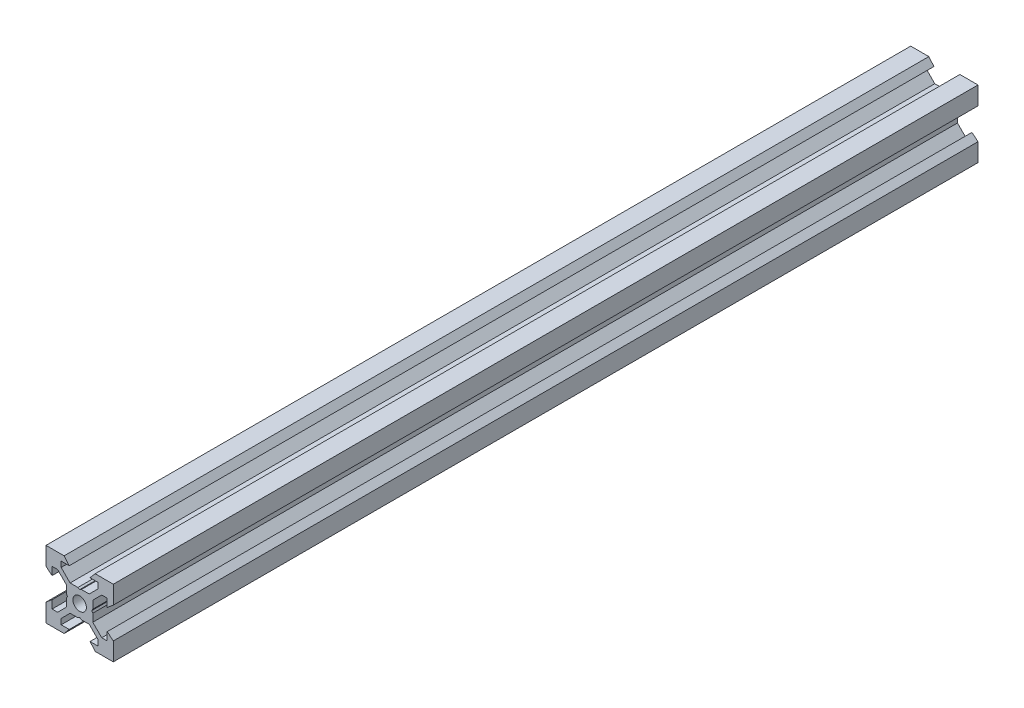
SolidWorks part; units mm, degrees
ref_plane "Front Plane" through (0, 0, 0) normal (0, 0, 1) x (1, 0, 0)
ref_plane "Top Plane" through (0, 0, 0) normal (0, 1, 0) x (1, 0, 0)
ref_plane "Right Plane" through (0, 0, 0) normal (1, 0, 0) x (0, 0, -1)
sketch "Sketch1" plane through (0, 0, 0) normal (0, 0, 1) x (1, 0, 0)
  line L0 (10, 10) -> (4.6104, 10) construction
  line L1 (10, 10) -> (10, 4.6104) construction
  line L2 (10, -10) -> (10, -4.6104) construction
  line L3 (10, -10) -> (4.6104, -10) construction
  line L4 (10, 10) -> (10, 4.6104)
  line L5 (6.5607, 5.5) -> (8.2, 5.5)
  line L6 (5.5, 8.2) -> (5.5, 6.5607)
  line L7 (10, 10) -> (4.6104, 10)
  line L8 (10, 10) -> (10, 4.6104)
  line L9 (6.5607, 5.5) -> (3.9, 2.8393)
  line L10 (5.5, 6.5607) -> (2.8393, 3.9)
  line L11 (10, 4.6104) -> (8.2, 3.1)
  line L12 (4.6104, 10) -> (3.1, 8.2)
  line L13 (8.2, 3.1) -> (8.2, 5.5)
  line L14 (3.1, 8.2) -> (5.5, 8.2)
  line L15 (-6.5607, 5.5) -> (-8.2, 5.5)
  line L16 (6.5607, -5.5) -> (8.2, -5.5)
  line L17 (3.1, -8.2) -> (5.5, -8.2)
  line L18 (8.2, -3.1) -> (8.2, -5.5)
  line L19 (4.6104, -10) -> (3.1, -8.2)
  line L20 (10, -4.6104) -> (8.2, -3.1)
  line L21 (0.5196, -3.9) -> (0, -3.6)
  line L22 (0.5196, 3.9) -> (0, 3.6)
  line L23 (3.6, 0) -> (3.9, -0.5196)
  line L24 (3.9, 0.5196) -> (3.6, 0)
  line L25 (3.9, 0.5196) -> (3.9, 2.8393)
  line L26 (2.8393, 3.9) -> (0.5196, 3.9)
  line L27 (3.9, -2.8393) -> (3.9, -0.5196)
  line L28 (2.8393, -3.9) -> (0.5196, -3.9)
  line L29 (5.5, -6.5607) -> (2.8393, -3.9)
  line L30 (6.5607, -5.5) -> (3.9, -2.8393)
  line L31 (10, -10) -> (10, -4.6104)
  line L32 (10, -10) -> (4.6104, -10)
  line L33 (5.5, -8.2) -> (5.5, -6.5607)
  line L34 (-6.5607, -5.5) -> (-8.2, -5.5)
  line L35 (10, -10) -> (10, -4.6104)
  line L36 (0, 0) -> (0, 8.2) construction
  line L37 (-10, -10) -> (-4.6104, -10) construction
  line L38 (-10, -10) -> (-10, -4.6104) construction
  line L39 (-10, 10) -> (-10, 4.6104) construction
  line L40 (-10, 10) -> (-4.6104, 10) construction
  line L41 (-10, -10) -> (-10, -4.6104)
  line L43 (-5.5, -8.2) -> (-5.5, -6.5607)
  line L44 (-10, -10) -> (-4.6104, -10)
  line L45 (-10, -10) -> (-10, -4.6104)
  line L46 (-6.5607, -5.5) -> (-3.9, -2.8393)
  line L47 (-5.5, -6.5607) -> (-2.8393, -3.9)
  line L48 (-2.8393, -3.9) -> (-0.5196, -3.9)
  line L49 (-3.9, -2.8393) -> (-3.9, -0.5196)
  line L50 (-2.8393, 3.9) -> (-0.5196, 3.9)
  line L51 (-3.9, 0.5196) -> (-3.9, 2.8393)
  line L52 (-3.9, 0.5196) -> (-3.6, 0)
  line L53 (-3.6, 0) -> (-3.9, -0.5196)
  line L54 (-0.5196, 3.9) -> (0, 3.6)
  line L55 (-0.5196, -3.9) -> (0, -3.6)
  line L56 (-10, -4.6104) -> (-8.2, -3.1)
  line L57 (-4.6104, -10) -> (-3.1, -8.2)
  line L58 (-8.2, -3.1) -> (-8.2, -5.5)
  line L59 (-3.1, -8.2) -> (-5.5, -8.2)
  line L60 (-10, -10) -> (10, -10) construction
  line L61 (-10, -10) -> (-10, 10) construction
  line L62 (-3.1, 8.2) -> (-5.5, 8.2)
  line L63 (-8.2, 3.1) -> (-8.2, 5.5)
  line L64 (-4.6104, 10) -> (-3.1, 8.2)
  line L65 (-10, 4.6104) -> (-8.2, 3.1)
  line L66 (-5.5, 6.5607) -> (-2.8393, 3.9)
  line L67 (-6.5607, 5.5) -> (-3.9, 2.8393)
  line L68 (-10, 10) -> (-10, 4.6104)
  line L69 (-10, 10) -> (-4.6104, 10)
  line L70 (-5.5, 8.2) -> (-5.5, 6.5607)
  line L71 (-10, 10) -> (10, 10) construction
  line L72 (-10, 10) -> (-10, 4.6104)
  line L73 (10, -10) -> (10, 10) construction
  line L74 (-10, -10) -> (10, 10) construction
  line L75 (-10, 10) -> (10, -10) construction
  circle A0 centre (0, 0) radius 2
  dimension "D7" = 4
  dimension "D1" = 20
  dimension "D2" = 5.3896
  dimension "D3" = 4.5
  dimension "D4" = 50
  dimension "D5" = 1.8
  dimension "D6" = 1.5104
  dimension "D8" = 5.5
  dimension "D9" = 120
  dimension "D10" = 0.3
  dimension "D11" = 2.3197
  dimension "D12" = 7.8
  dimension "D13" = 7.8
  dimension "D14" = 1.5
  dimension "D15" = 2.6607
extrude "Boss-Extrude1" add sketch "Sketch1" along normal mid plane 257 contours L70 L62 L64 L69 L68 L65 L63 L15 L67 L51 L52 L53 L49 L46 L34 L58 L56 L41 L44 L57 L59 L43 L47 L48 L55 L21 L28 L29 L33 L17 L19 L32 L31 L20 L18 L16 L30 L27 L23 L24 L25 L9 L5 L13 L11 L4 L7 L12 L14 L6 L10
